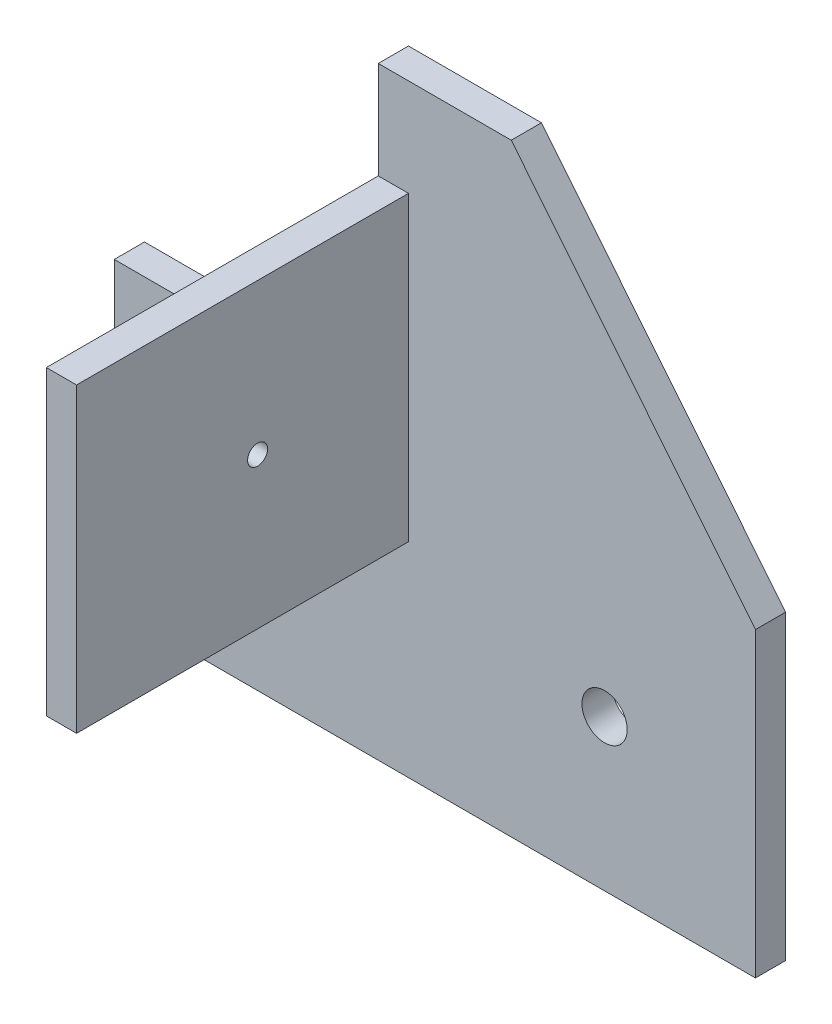
SolidWorks part; units mm, degrees
ref_plane "Ebene vorne" through (0, 0, 0) normal (0, 0, 1) x (1, 0, 0)
ref_plane "Ebene oben" through (0, 0, 0) normal (0, 1, 0) x (1, 0, 0)
ref_plane "Ebene rechts" through (0, 0, 0) normal (1, 0, 0) x (0, 0, -1)
sketch "Skizze1" plane through (0, 0, 0) normal (0, 0, 1) x (1, 0, 0)
  line L0 (-78.1323, 0) -> (-43.1323, 0)
  line L1 (-43.1323, 0) -> (-43.1323, 40)
  line L2 (-43.1323, 40) -> (-25.5058, 40)
  line L3 (-25.5058, 40) -> (6.8677, 0)
  line L4 (6.8677, 0) -> (6.8677, -40)
  line L5 (6.8677, -40) -> (-78.1323, -40)
  line L6 (-78.1323, -40) -> (-78.1323, 0)
  line L7 (6.8677, -40) -> (-33.1323, -40) construction
  line L8 (-33.1323, -40) -> (6.8677, 0) construction
  line L9 (6.8677, -40) -> (-13.1323, -20) construction
  circle A0 centre (-13.1323, -20) radius 3
  dimension "D7" = 6
  dimension "D1" = 40
  dimension "D2" = 40
  dimension "D3" = 35
  dimension "D4" = 50
  dimension "D5" = 40
  dimension "D6" = 40
extrude "Aufsatz-Linear austragen1" add sketch "Skizze1" along normal blind 4
sketch "Skizze3" plane through (-43.1323, 0, 0) normal (-1, 0, 0) x (0, 0, 1)
  line L0 (0, 40) -> (0, 0) construction
  line L1 (48, -12.9144) -> (0, -12.9144)
  line L2 (48, -12.9144) -> (48, 27.0856)
  line L3 (48, 27.0856) -> (0, 27.0856)
  line L4 (0, -12.9144) -> (0, 27.0856)
  line L6 (48, -12.9144) -> (0, 27.0856) construction
  line L7 (48, 27.0856) -> (0, -12.9144) construction
  circle A0 centre (24, 7.0856) radius 1.3249
  dimension "D1" = 48
  dimension "D2" = 40
extrude "Aufsatz-Linear austragen2" add sketch "Skizze3" against normal blind 4
